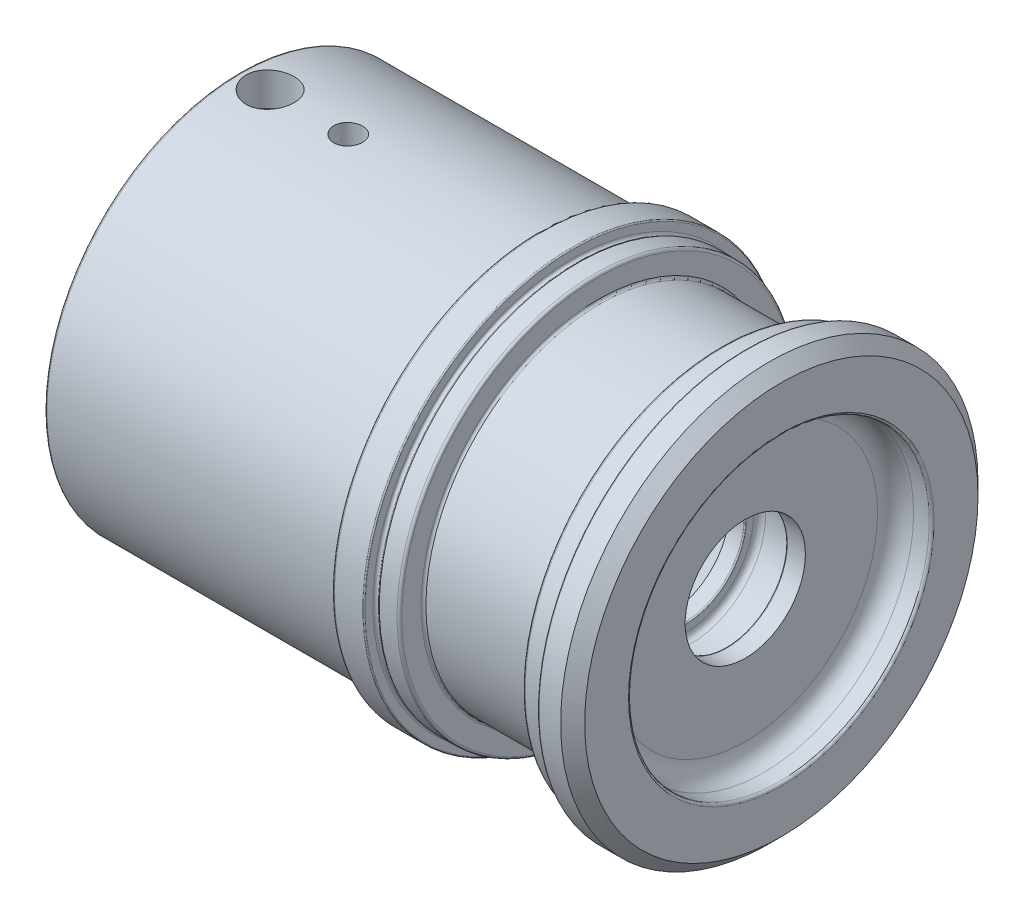
SolidWorks part; units mm, degrees
ref_plane "Front" through (0, 0, 0) normal (0, 0, 1) x (1, 0, 0)
ref_plane "Top" through (0, 0, 0) normal (0, 1, 0) x (1, 0, 0)
ref_plane "Right" through (0, 0, 0) normal (1, 0, 0) x (0, 0, -1)
sketch "Sketch1" plane through (0, 0, 0) normal (0, 0, 1) x (1, 0, 0)
  line L0 (0, 0) -> (0, 71.1326) construction
  line L1 (0, 0) -> (-126.7161, 0) construction
  line L2 (0, 25.4) -> (0, 32.7)
  line L3 (-2, 34.7) -> (-5.6, 34.7)
  line L4 (-5.8, 34.5) -> (-5.8, 33.2)
  line L5 (-6.6536, 33) -> (-9.6, 33)
  line L6 (-10, 32.6) -> (-10, 29.4)
  line L7 (-10.4, 29) -> (-30.1, 29)
  line L8 (-30.5, 29.4) -> (-30.5, 32.6)
  line L9 (-30.9, 33) -> (-33.8464, 33)
  line L10 (-34.7, 33.2) -> (-34.7, 34.5)
  line L11 (-34.9, 34.7) -> (-39.6, 34.7)
  line L12 (-29, 22.5) -> (-29.7231, 22.9175)
  line L13 (-40.4, 32.5) -> (-89.6, 32.5)
  line L14 (-90, 32.1) -> (-90, 27.4)
  line L15 (-89.6, 27) -> (-80, 27)
  line L16 (-80, 27) -> (-80, 25)
  line L17 (-80, 25) -> (-63, 25)
  line L18 (-63, 25) -> (-59.393, 22.9175)
  line L19 (-59.393, 22.9175) -> (-29.7231, 22.9175)
  line L20 (-2, 34.7) -> (0, 32.7)
  line L21 (-29, 22.5) -> (-23.4, 22.5)
  line L22 (-23, 22.1) -> (-23, 12.5)
  line L23 (-40, 32.9) -> (-40, 34.3)
  line L24 (-6, 10) -> (-6, 22)
  line L25 (-3, 25) -> (-0.4, 25)
  line L26 (-23, 12.5) -> (-18.6699, 10)
  line L27 (-18.6699, 10) -> (-16.2, 10)
  line L28 (-16, 10.2) -> (-16, 11.4)
  line L29 (-15, 12.4) -> (-10.2, 12.4)
  line L30 (-9.2, 11.4) -> (-9.2, 10.2)
  line L31 (-9, 10) -> (-6, 10)
  line L32 (-6.4, 32.8536) -> (-6.6536, 33)
  line L33 (-34.1, 32.8536) -> (-33.8464, 33)
  arc A0 (-34.7, 34.5) -> (-34.9, 34.7) centre (-34.9, 34.5) ccw
  arc A1 (-34.7, 33.2) -> (-34.1, 32.8536) centre (-34.3, 33.2) ccw
  arc A2 (-30.5, 32.6) -> (-30.9, 33) centre (-30.9, 32.6) ccw
  arc A3 (-30.1, 29) -> (-30.5, 29.4) centre (-30.1, 29.4) cw
  arc A4 (-10, 29.4) -> (-10.4, 29) centre (-10.4, 29.4) cw
  arc A5 (-9.6, 33) -> (-10, 32.6) centre (-9.6, 32.6) ccw
  arc A6 (-5.8, 33.2) -> (-6.4, 32.8536) centre (-6.2, 33.2) cw
  arc A7 (-5.6, 34.7) -> (-5.8, 34.5) centre (-5.6, 34.5) ccw
  arc A8 (-89.6, 32.5) -> (-90, 32.1) centre (-89.6, 32.1) ccw
  arc A9 (-90, 27.4) -> (-89.6, 27) centre (-89.6, 27.4) ccw
  arc A10 (0, 25.4) -> (-0.4, 25) centre (-0.4, 25.4) cw
  arc A11 (-6, 22) -> (-3, 25) centre (-3, 22) cw
  arc A12 (-40, 32.9) -> (-40.4, 32.5) centre (-40.4, 32.9) cw
  arc A13 (-40, 34.3) -> (-39.6, 34.7) centre (-39.6, 34.3) cw
  arc A16 (-16, 10.2) -> (-16.2, 10) centre (-16.2, 10.2) cw
  arc A17 (-9, 10) -> (-9.2, 10.2) centre (-9, 10.2) cw
  arc A18 (-23.4, 22.5) -> (-23, 22.1) centre (-23.4, 22.1) cw
  arc A19 (-15, 12.4) -> (-16, 11.4) centre (-15, 11.4) ccw
  arc A20 (-9.2, 11.4) -> (-10.2, 12.4) centre (-10.2, 11.4) ccw
  point P56 (0, 25)
  point P61 (-40, 32.5)
  dimension "D29" = 0.2
  dimension "D32" = 0.4
  dimension "D28" = 0.4
  dimension "D33" = 3
  dimension "D35" = 0.2
  dimension "D36" = 0.4
  dimension "D37" = 0.4
  dimension "D39" = 0.4
  dimension "D43" = 0.4
  dimension "D45" = 1
  dimension "D1" = 66
  dimension "D2" = 58
  dimension "D3" = 69.4
  dimension "D4" = 45.835
  dimension "D5" = 45
  dimension "D6" = 30
  dimension "D7" = 6
  dimension "D8" = 90
  dimension "D9" = 54
  dimension "D10" = 10
  dimension "D11" = 27
  dimension "D12" = 50
  dimension "D13" = 30
  dimension "D14" = 67
  dimension "D15" = 20.5
  dimension "D16" = 4.2
  dimension "D17" = 10
  dimension "D18" = 6
  dimension "D19" = 50
  dimension "D20" = 50
  dimension "D21" = 65
  dimension "D22" = 20
  dimension "D23" = 24.8
  dimension "D24" = 16
  dimension "D25" = 6.8
  dimension "D26" = 30
  dimension "D27" = 25
  dimension "D30" = 45
  dimension "D31" = 2
  dimension "D38" = 30
  dimension "D40" = 0.2
  dimension "D41" = 4.2
  dimension "D42" = 30
  dimension "D44" = 0.2
revolve "Base-Revolve" add sketch "Sketch1" angle 360 about L1
cosmetic thread "Cosmetic Thread1" parameters "D1"=30, "D2"=48
sketch "Sketch2" plane through (0, 0, 0) normal (0, 1, 0) x (1, 0, 0)
  line L0 (-90, 32.5) -> (-90, -32.5) construction
  circle A0 centre (-85, 0) radius 4
  dimension "D2" = 8
  dimension "D1" = 5
extrude "Cut-Extrude2" cut sketch "Sketch2" against normal mid plane 81
sketch "Sketch3" plane through (0, 0, 0) normal (0, 1, 0) x (1, 0, 0)
  line L0 (0, 0) -> (-126.7161, 0) construction
  line L1 (-90, 32.5) -> (-90, -32.5) construction
  circle A0 centre (-72, 0) radius 2.4
  dimension "D2" = 4.8
  dimension "D1" = 18
extrude "Cut-Extrude3" cut sketch "Sketch3" along normal blind 40.5
cosmetic thread "Cosmetic Thread2" parameters "D1"=7.6155, "D2"=6
